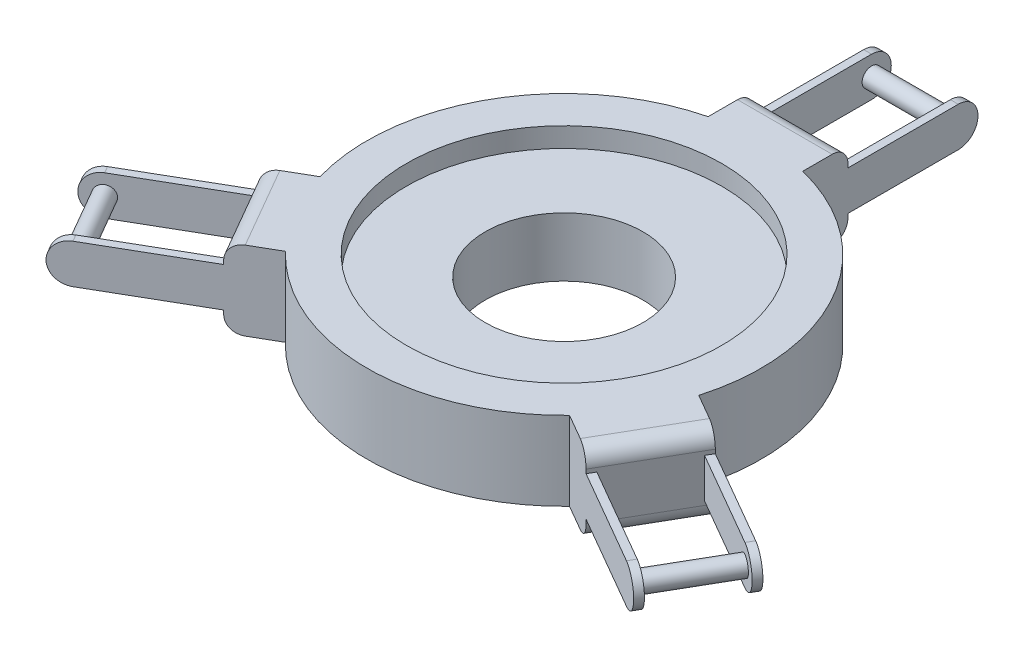
SolidWorks part; units mm, degrees
ref_plane "Front Plane" through (0, 0, 0) normal (0, 0, 1) x (1, 0, 0)
ref_plane "Top Plane" through (0, 0, 0) normal (0, 1, 0) x (1, 0, 0)
ref_plane "Right Plane" through (0, 0, 0) normal (1, 0, 0) x (0, 0, -1)
sketch "Sketch1" plane through (0, 0, 0) normal (0, 1, 0) x (1, 0, 0)
  line L1 (0, 150) -> (-30, 150)
  line L2 (-30, 150) -> (-30, 121.3466)
  line L4 (30, 121.3466) -> (30, 150)
  line L5 (30, 150) -> (0, 150)
  line L6 (144.9038, -49.0192) -> (120.0892, -34.6925)
  line L7 (129.9038, -75) -> (144.9038, -49.0192)
  line L8 (114.9038, -100.9808) -> (129.9038, -75)
  line L9 (90.0892, -86.6541) -> (114.9038, -100.9808)
  line L10 (-114.9038, -100.9808) -> (-90.0892, -86.6541)
  line L11 (-129.9038, -75) -> (-114.9038, -100.9808)
  line L12 (-144.9038, -49.0192) -> (-129.9038, -75)
  line L13 (-120.0892, -34.6925) -> (-144.9038, -49.0192)
  arc A0 (-30, 121.3466) -> (-120.0892, -34.6925) centre (0, 0) ccw
  arc A1 (-90.0892, -86.6541) -> (90.0892, -86.6541) centre (0, 0) ccw
  arc A2 (120.0892, -34.6925) -> (30, 121.3466) centre (0, 0) ccw
  point P20 (0, 0)
  dimension "D1" = 150
  dimension "D2" = 250
  dimension "D3" = 3
  dimension "D4" = 30
extrude "Boss-Extrude1" add sketch "Sketch1" along normal blind 50
sketch "Sketch3" plane through (0, 50, 0) normal (0, 1, 0) x (1, 0, 0)
  circle A0 centre (0, 0) radius 50
extrude "Cut-Extrude1" cut sketch "Sketch3" against normal blind 50
sketch "Sketch4" plane through (0, 0, 0) normal (1, 0, 0) x (0, 0, -1)
  line L0 (150, 25) -> (202.8367, 25) construction
  line L1 (150, 37.5) -> (220, 37.5)
  line L2 (220, 12.5) -> (150, 12.5)
  line L3 (138.5596, 19.9635) -> (139.8707, 17.6756) construction
  line L4 (171.6608, 14.2178) -> (180, 0) construction
  arc A0 (150, 37.5) -> (150, 12.5) centre (150, 25) ccw
  arc A1 (220, 12.5) -> (220, 37.5) centre (220, 25) ccw
  dimension "D2" = 25
  dimension "D3" = 25
  dimension "D1" = 70
extrude "Boss-Extrude2" add sketch "Sketch4" along normal blind 5 from offset 25
mirror "Mirror1" about plane through (0, 0, 0) normal (1, 0, 0) of "Boss-Extrude2"
fillet "Fillet1" radius 10 6 edges at (-129.9038, 50, 75) (-129.9038, 0, 75) (129.9038, 0, 75) (129.9038, 50, 75) (0, 0, -150) (0, 50, -150)
sketch "Sketch6" plane through (0, 50, 0) normal (0, 1, 0) x (1, 0, 0)
  circle A0 centre (0, 0) radius 100
extrude "Cut-Extrude2" cut sketch "Sketch6" against normal blind 12.5
sketch "Sketch7" plane through (0, 0, 0) normal (1, 0, 0) x (0, 0, -1)
  line L7 (121.3466, 0) -> (140, 0)
  line L8 (150, 10) -> (150, 12.5)
  line L9 (150, 12.5) -> (220, 12.5)
  line L10 (220, 37.5) -> (150, 37.5)
  line L11 (150, 37.5) -> (150, 40)
  line L12 (140, 50) -> (121.3466, 50)
  line L13 (121.3466, 50) -> (121.3466, 0)
  line L14 (121.3466, 0) -> (140, 0) construction
  line L15 (150, 10) -> (150, 12.5) construction
  line L16 (150, 12.5) -> (220, 12.5) construction
  line L17 (220, 37.5) -> (150, 37.5) construction
  line L18 (150, 37.5) -> (150, 40) construction
  line L19 (140, 50) -> (121.3466, 50) construction
  line L20 (121.3466, 50) -> (121.3466, 0) construction
  circle A0 centre (220, 25) radius 6
  arc A3 (140, 0) -> (150, 10) centre (140, 10) ccw
  arc A4 (220, 12.5) -> (220, 37.5) centre (220, 25) ccw
  arc A5 (150, 40) -> (140, 50) centre (140, 40) ccw
  arc A6 (140, 0) -> (150, 10) centre (140, 10) ccw construction
  arc A7 (220, 12.5) -> (220, 37.5) centre (220, 25) ccw construction
  arc A8 (150, 40) -> (140, 50) centre (140, 40) ccw construction
  dimension "D2" = 12
  dimension "D1" = 0
extrude "Boss-Extrude3" add sketch "Sketch7" along normal blind 25 and the other way blind 26
pattern_circular "CirPattern1" count 3 over 360 about axis through (0, 0, 0) along (0, 1, 0) of "Boss-Extrude3", "Boss-Extrude2", "Mirror1"
